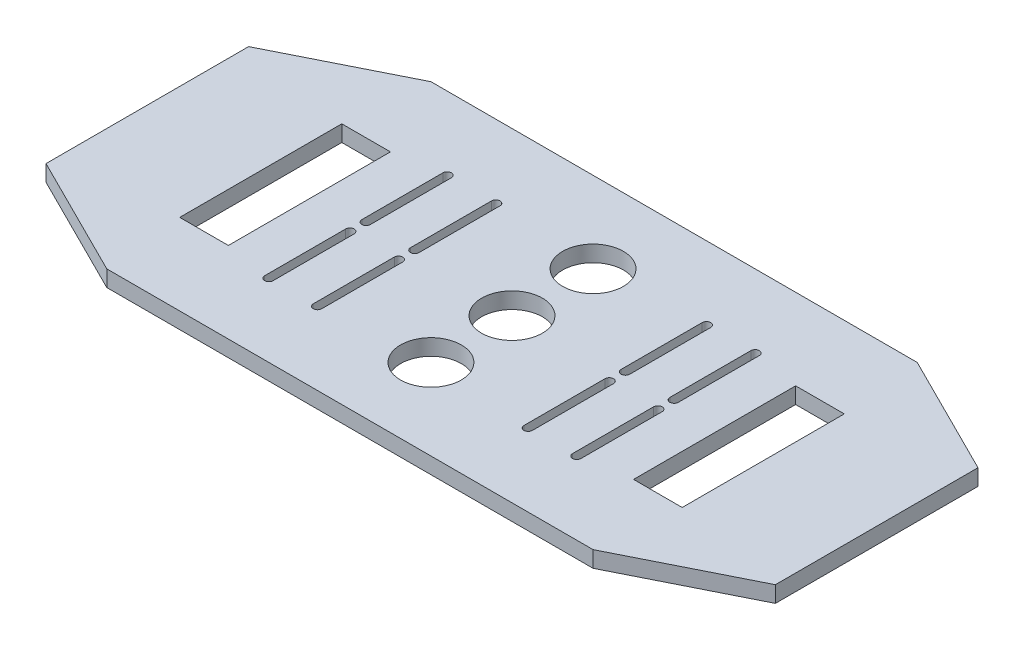
SolidWorks part; units mm, degrees
material "Pin"
ref_plane "Plan de face" through (0, 0, 0) normal (0, 0, 1) x (1, 0, 0)
ref_plane "Plan de dessus" through (0, 0, 0) normal (0, 1, 0) x (1, 0, 0)
ref_plane "Plan de droite" through (0, 0, 0) normal (1, 0, 0) x (0, 0, -1)
sketch "Esquisse1" plane through (0, 0, 0) normal (0, 1, 0) x (1, 0, 0)
  line L1 (0, 0) -> (180, 0)
  line L2 (0, 0) -> (0, 80)
  line L3 (0, 80) -> (180, 80)
  line L4 (180, 0) -> (180, 80)
  dimension "D1" = 80
  dimension "D2" = 180
extrude "Boss.-Extru.1" add sketch "Esquisse1" along normal blind 4
sketch "Esquisse2" plane through (0, 4, 0) normal (0, 1, 0) x (1, 0, 0)
  line L0 (30, 0) -> (0, 15)
  line L1 (0, 0) -> (180, 0) construction
  line L2 (0, 80) -> (0, 0) construction
  line L3 (0, 15) -> (0, 0)
  line L4 (0, 0) -> (30, 0)
  line L5 (30, 80) -> (0, 65)
  line L6 (180, 80) -> (0, 80) construction
  line L7 (0, 65) -> (0, 80)
  line L8 (0, 80) -> (30, 80)
  line L9 (150, 0) -> (180, 15)
  line L10 (180, 0) -> (180, 80) construction
  line L11 (180, 15) -> (180, 0)
  line L12 (180, 0) -> (150, 0)
  line L13 (150, 80) -> (180, 80)
  line L14 (180, 80) -> (180, 65)
  line L15 (180, 65) -> (150, 80)
  dimension "D1" = 15
  dimension "D2" = 30
  dimension "D3" = 30
  dimension "D4" = 15
  dimension "D5" = 15
  dimension "D6" = 30
  dimension "D7" = 30
  dimension "D8" = 15
extrude "Enlèv. mat.-Extru.1" cut sketch "Esquisse2" against normal blind 4
sketch "Esquisse3" plane through (0, 4, 0) normal (0, 1, 0) x (1, 0, 0)
  line L0 (8.5147, 40) -> (227.2024, 40) construction
  line L1 (30, 0) -> (150, 0) construction
  line L2 (90, 126.5747) -> (90, -53.3594) construction
  line L3 (150, 80) -> (30, 80) construction
  line L4 (0, 65) -> (0, 15) construction
  line L5 (64, 38) -> (64, 18) construction
  line L6 (65.05, 38) -> (65.05, 18)
  line L7 (62.95, 38) -> (62.95, 18)
  line L8 (52, 18) -> (52, 38) construction
  line L9 (50.95, 18) -> (50.95, 38)
  line L10 (53.05, 18) -> (53.05, 38)
  line L11 (128, 18) -> (128, 38) construction
  line L12 (129.05, 18) -> (129.05, 38)
  line L13 (126.95, 18) -> (126.95, 38)
  line L14 (116, 38) -> (116, 18) construction
  line L15 (114.95, 38) -> (114.95, 18)
  line L16 (117.05, 38) -> (117.05, 18)
  line L17 (52, 62) -> (52, 42) construction
  line L18 (50.95, 62) -> (50.95, 42)
  line L19 (53.05, 62) -> (53.05, 42)
  line L20 (64, 42) -> (64, 62) construction
  line L21 (65.05, 42) -> (65.05, 62)
  line L22 (62.95, 42) -> (62.95, 62)
  line L23 (116, 42) -> (116, 62) construction
  line L24 (114.95, 42) -> (114.95, 62)
  line L25 (117.05, 42) -> (117.05, 62)
  line L26 (128, 62) -> (128, 42) construction
  line L27 (129.05, 62) -> (129.05, 42)
  line L28 (126.95, 62) -> (126.95, 42)
  arc A0 (65.05, 38) -> (62.95, 38) centre (64, 38) ccw
  arc A1 (62.95, 18) -> (65.05, 18) centre (64, 18) ccw
  arc A2 (50.95, 18) -> (53.05, 18) centre (52, 18) ccw
  arc A3 (53.05, 38) -> (50.95, 38) centre (52, 38) ccw
  arc A4 (129.05, 18) -> (126.95, 18) centre (128, 18) cw
  arc A5 (126.95, 38) -> (129.05, 38) centre (128, 38) cw
  arc A6 (114.95, 38) -> (117.05, 38) centre (116, 38) cw
  arc A7 (117.05, 18) -> (114.95, 18) centre (116, 18) cw
  arc A8 (50.95, 62) -> (53.05, 62) centre (52, 62) cw
  arc A9 (53.05, 42) -> (50.95, 42) centre (52, 42) cw
  arc A10 (65.05, 42) -> (62.95, 42) centre (64, 42) cw
  arc A11 (62.95, 62) -> (65.05, 62) centre (64, 62) cw
  arc A12 (114.95, 42) -> (117.05, 42) centre (116, 42) ccw
  arc A13 (117.05, 62) -> (114.95, 62) centre (116, 62) ccw
  arc A14 (129.05, 62) -> (126.95, 62) centre (128, 62) ccw
  arc A15 (126.95, 42) -> (129.05, 42) centre (128, 42) ccw
  point P12 (64, 28)
  point P17 (52, 28)
  point P26 (128, 28)
  point P33 (116, 28)
  point P40 (52, 52)
  point P47 (64, 52)
  point P54 (116, 52)
  point P61 (128, 52)
  dimension "D1" = 40
  dimension "D2" = 90
  dimension "D3" = 20
  dimension "D4" = 20
  dimension "D5" = 2.1
  dimension "D6" = 2.1
  dimension "D7" = 12
  dimension "D8" = 12
  dimension "D9" = 12
  dimension "D10" = 26
extrude "Enlèv. mat.-Extru.2" cut sketch "Esquisse3" against normal blind 4
ref_plane "Plan8" through (90, 0, 0) normal (-1, 0, 0) x (0, 0, 1)
sketch "Esquisse11" plane through (0, 4, 0) normal (0, 1, 0) x (1, 0, 0)
  line L0 (0, 65) -> (0, 15) construction
  line L1 (28, 60) -> (40, 60)
  line L2 (28, 60) -> (28, 20)
  line L3 (28, 20) -> (40, 20)
  line L4 (40, 60) -> (40, 20)
  line L5 (30, 0) -> (150, 0) construction
  line L6 (150, 80) -> (30, 80) construction
  line L7 (90, 111.4033) -> (90, -12.0266) construction
  line L8 (152, 20) -> (140, 20)
  line L9 (140, 60) -> (140, 20)
  line L10 (152, 60) -> (140, 60)
  line L11 (152, 60) -> (152, 20)
  dimension "D1" = 12
  dimension "D2" = 28
  dimension "D3" = 20
  dimension "D4" = 20
  dimension "D5" = 90
extrude "Enlèv. mat.-Extru.5" cut sketch "Esquisse11" against normal up to next and the other way through all
sketch "Esquisse14" plane through (0, 4, 0) normal (0, 1, 0) x (1, 0, 0)
  line L0 (30, 0) -> (150, 0) construction
  line L1 (0, 65) -> (0, 15) construction
  circle A0 centre (90, 60) radius 7.5
  circle A1 centre (90, 40) radius 7.5
  circle A2 centre (90, 20) radius 7.5
  dimension "D1" = 15
  dimension "D2" = 15
  dimension "D3" = 15
  dimension "D4" = 40
  dimension "D5" = 20
  dimension "D6" = 20
  dimension "D7" = 90
extrude "Enlèv. mat.-Extru.6" cut sketch "Esquisse14" against normal up to next
equation "\"D8@Esquisse2\"=\"D1@Esquisse2\""
equation "\"D4@Esquisse2\"=\"D1@Esquisse2\""
equation "\"D5@Esquisse2\"=\"D1@Esquisse2\""
